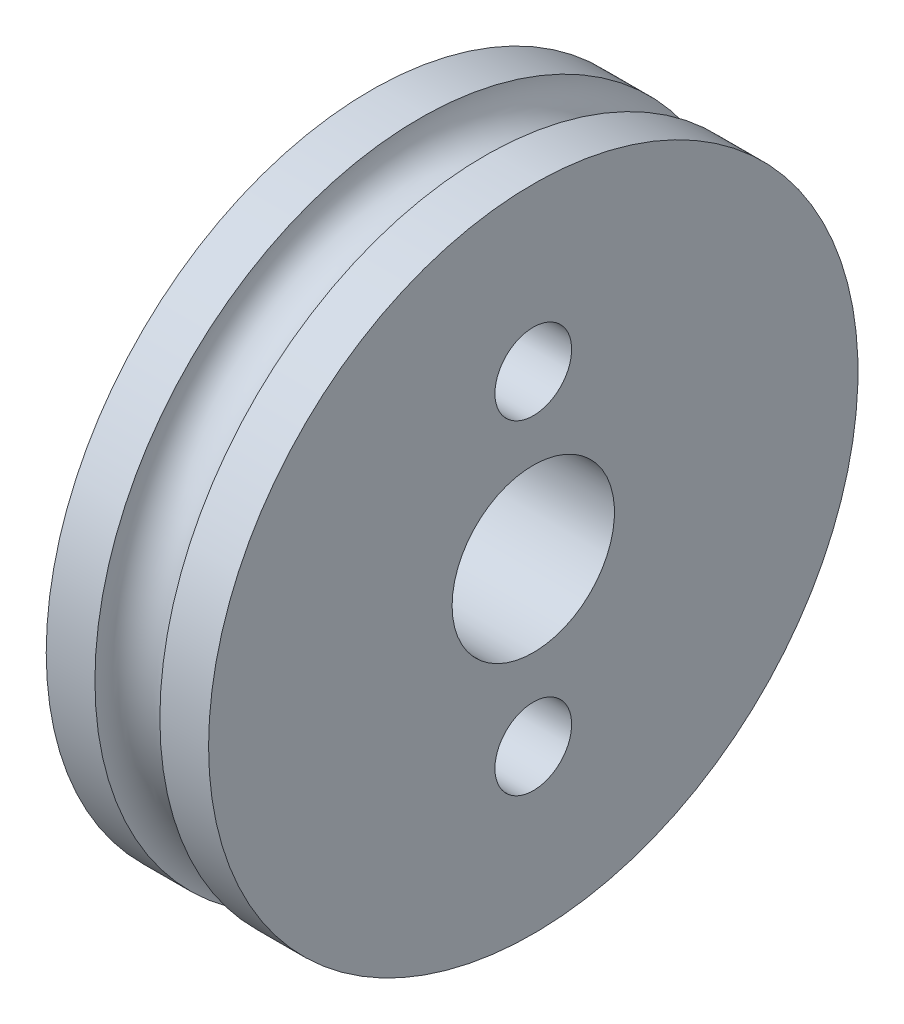
SolidWorks part; units mm, degrees
ref_plane "Front Plane" through (0, 0, 0) normal (0, 0, 1) x (1, 0, 0)
ref_plane "Top Plane" through (0, 0, 0) normal (0, 1, 0) x (1, 0, 0)
ref_plane "Right Plane" through (0, 0, 0) normal (1, 0, 0) x (0, 0, -1)
sketch "Sketch1" plane through (0, 0, 0) normal (0, 0, 1) x (1, 0, 0)
  line L0 (0, 0) -> (34.464, 0) construction
  line L1 (0, 3.175) -> (6.35, 3.175)
  line L2 (6.35, 3.175) -> (6.35, 12.7)
  line L3 (6.35, 12.7) -> (4.445, 12.7)
  line L4 (0, 3.175) -> (0, 12.7)
  line L5 (0, 12.7) -> (1.905, 12.7)
  arc A0 (1.905, 12.7) -> (4.445, 12.7) centre (3.175, 12.7) ccw
  point P14 (3.175, 3.175)
  dimension "D3" = 1.27
  dimension "D1" = 6.35
  dimension "D2" = 6.35
  dimension "D4" = 25.4
revolve "Revolve1" add sketch "Sketch1" angle 360 about L0
sketch "Sketch2" plane through (0, 0, 0) normal (1, 0, 0) x (0, 0, -1)
  line L0 (0, 0) -> (16.2936, 0) construction
  circle A0 centre (0, 6.35) radius 1.7343 construction
  circle A1 centre (0, -6.35) radius 1.7343 construction
  dimension "D1" = 12.7
hole_wizard "Ø3.0mm Dowel Hole1" positions "Sketch3" profile "Sketch4" hole size "Ø3.0" standard "ANSI Metric" end condition through all
sketch "Sketch3" plane through (0, 0, 0) normal (-1, 0, 0) x (0, 0, 1)
  point P0 (0, 6.35)
  point P3 (0, -6.35)
sketch "Sketch4" plane through (0, 6.35, 0) normal (0, 1, 0) x (0, 0, 1)
  line L0 (0, 0) -> (0, 6.35)
  line L1 (0, 6.35) -> (1.5, 6.35)
  line L2 (1.5, 6.35) -> (1.5, 0.025)
  line L3 (1.5, 0.025) -> (1.525, 0)
  line L5 (1.525, 0) -> (0, 0)
  line L6 (-1.5, 0.025) -> (-1.525, 0) construction
  line L11 (0, -6.35) -> (0, 107.95) construction
  dimension "Thru Hole Dia." = 3
  dimension "Thru Hole Depth" = 6.35
  dimension "Near C'Sink Dia." = 3.05
  dimension "Near C'Sink Angle" = 90
equation "\"width\" = 6in 'side to side 6"
equation "\"height\"= 1.25in'top to bottom from 1.25"
equation "\"length\"=6.25in 'back to front 6.25"
equation "\"side_width\"= 1in"
equation "\"wheel_di\"=1.875in'2.375"
equation "\"wepon_di\" = 1.25in ' milled rectangle must compensate for bolts ~ - .5 1.5"
equation "\"wepon_axle\" = 0.1in ' placement from front .5"
equation "\"frame_bolts\" = 0.125"
equation "\"wheel_base\"= 2.5in"
equation "\"cheesing\" = .25in ' width of general trusses"
